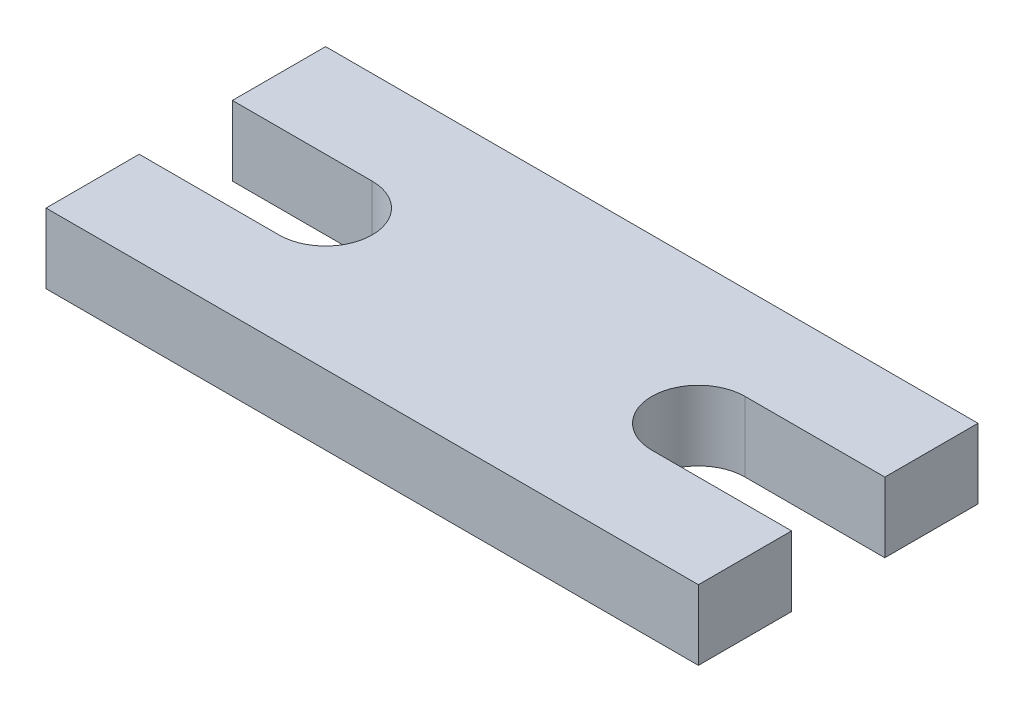
SolidWorks part; units mm, degrees
ref_plane "Front Plane" through (0, 0, 0) normal (0, 0, 1) x (1, 0, 0)
ref_plane "Top Plane" through (0, 0, 0) normal (0, 1, 0) x (1, 0, 0)
ref_plane "Right Plane" through (0, 0, 0) normal (1, 0, 0) x (0, 0, -1)
sketch "Sketch1" plane through (0, 0, 0) normal (0, 1, 0) x (1, 0, 0)
  line L1 (0, 0) -> (22.225, 0)
  line L2 (0, 0) -> (0, 9.525)
  line L3 (0, 9.525) -> (22.225, 9.525)
  line L4 (22.225, 0) -> (22.225, 9.525)
  dimension "D1" = 22.225
  dimension "D2" = 9.525
extrude "Boss-Extrude1" add sketch "Sketch1" along normal blind 2.3813
sketch "Sketch2" plane through (0, 2.3813, 0) normal (0, 1, 0) x (1, 0, 0)
  line L0 (22.225, 0) -> (22.225, 9.525) construction
  line L1 (0, 3.175) -> (4.7625, 3.175)
  line L2 (0, 3.175) -> (0, 6.35)
  line L3 (0, 6.35) -> (4.7625, 6.35)
  line L5 (22.225, 6.35) -> (22.225, 3.175)
  line L6 (17.4625, 3.175) -> (22.225, 3.175)
  line L8 (17.4625, 6.35) -> (22.225, 6.35)
  line L9 (0, 9.525) -> (0, 0) construction
  arc A0 (4.7625, 6.35) -> (4.7625, 3.175) centre (4.7625, 4.7625) cw
  arc A1 (17.4625, 3.175) -> (17.4625, 6.35) centre (17.4625, 4.7625) cw
  point P12 (0, 4.7625)
  point P15 (0, 4.7625)
  dimension "D3" = 1.5875
  dimension "D1" = 3.175
  dimension "D2" = 4.7625
extrude "Cut-Extrude1" cut sketch "Sketch2" against normal through all
